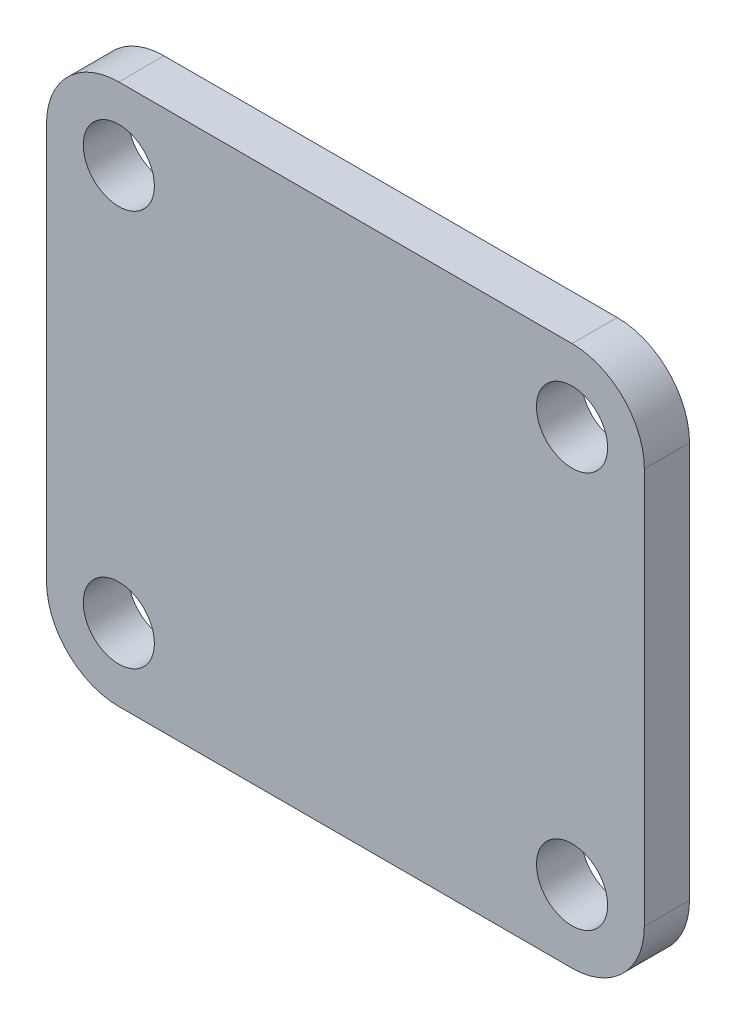
SolidWorks part; units mm, degrees
ref_plane "Plane1" through (0, 0, 0) normal (0, 0, 1) x (1, 0, 0)
ref_plane "Plane2" through (0, 0, 0) normal (0, 1, 0) x (1, 0, 0)
ref_plane "Plane3" through (0, 0, 0) normal (1, 0, 0) x (0, 0, -1)
sketch "Sketch1" plane through (0, 0, 0) normal (0, 0, 1) x (1, 0, 0)
  line L1 (7.96, -9.5) -> (-7.96, -9.5)
  line L2 (10.5, -6.96) -> (10.5, 6.96)
  line L3 (7.96, 9.5) -> (-7.96, 9.5)
  line L4 (-10.5, -6.96) -> (-10.5, 6.96)
  line L5 (10.5, -9.5) -> (-10.5, 9.5) construction
  line L6 (10.5, 9.5) -> (-10.5, -9.5) construction
  arc A0 (-7.96, -9.5) -> (-10.5, -6.96) centre (-7.96, -6.96) cw
  arc A1 (7.96, -9.5) -> (10.5, -6.96) centre (7.96, -6.96) ccw
  arc A2 (10.5, 6.96) -> (7.96, 9.5) centre (7.96, 6.96) ccw
  arc A3 (-7.96, 9.5) -> (-10.5, 6.96) centre (-7.96, 6.96) ccw
  point P0 (0, 0)
  dimension "D3" = 2.54
  dimension "D1" = 21
  dimension "D2" = 19
extrude "Boss-Extrude1" add sketch "Sketch1" along normal blind 1.5875
sketch "Sketch2" plane through (0, 0, 1.5875) normal (0, 0, 1) x (1, 0, 0)
  circle A0 centre (-7.96, 6.96) radius 1.25
  circle A1 centre (7.96, 6.96) radius 1.25
  circle A2 centre (7.96, -6.96) radius 1.25
  circle A3 centre (-7.96, -6.96) radius 1.25
  point P11 (-7.96, -6.96)
  dimension "D1" = 2.5
extrude "Cut-Extrude1" cut sketch "Sketch2" against normal through all
